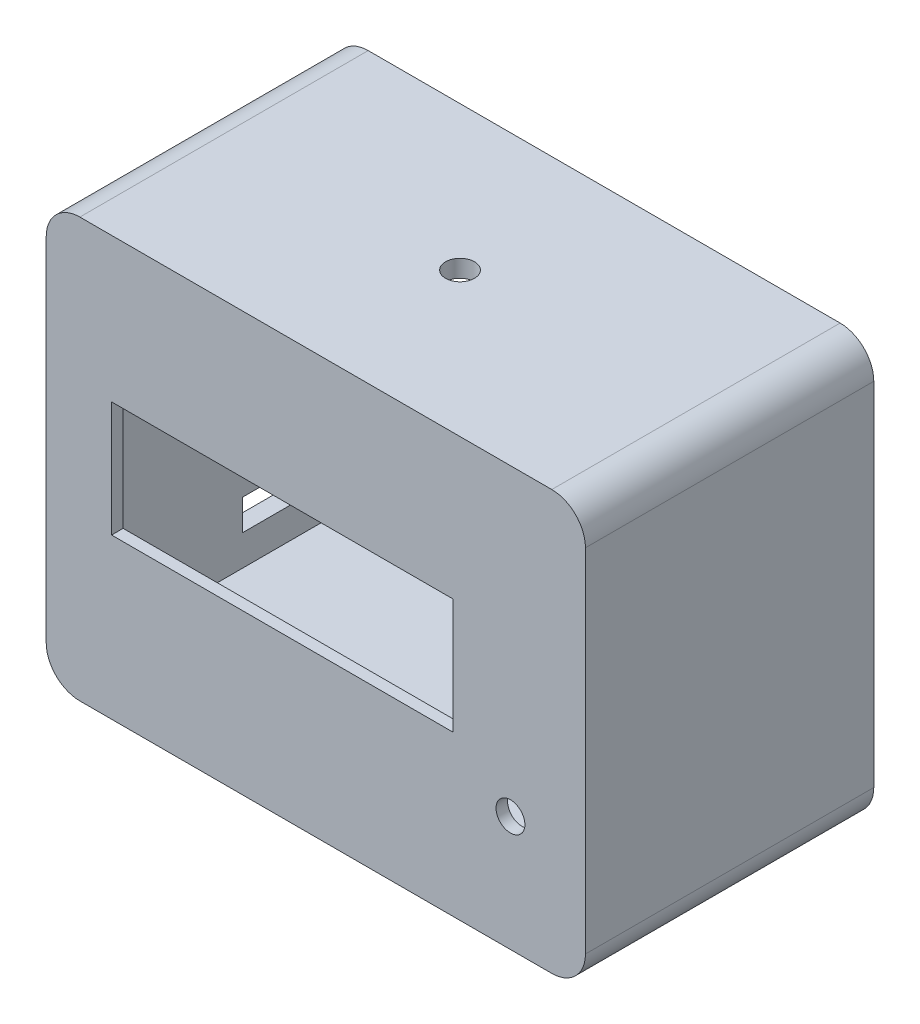
SolidWorks part; units mm, degrees
ref_plane "Front Plane" through (0, 0, 0) normal (0, 0, 1) x (1, 0, 0)
ref_plane "Top Plane" through (0, 0, 0) normal (0, 1, 0) x (1, 0, 0)
ref_plane "Right Plane" through (0, 0, 0) normal (1, 0, 0) x (0, 0, -1)
sketch "Sketch2" plane through (0, 0, 0) normal (0, 0, 1) x (1, 0, 0)
  line L1 (-52.8514, 50.3831) -> (59.3486, 50.3831)
  line L2 (-52.8514, 50.3831) -> (-52.8514, -36.8169)
  line L3 (-52.8514, -36.8169) -> (59.3486, -36.8169)
  line L4 (59.3486, 50.3831) -> (59.3486, -36.8169)
  line L5 (-39.2514, 20.3831) -> (31.7486, 20.3831)
  line L6 (-39.2514, 20.3831) -> (-39.2514, -3.6169)
  line L7 (-39.2514, -3.6169) -> (31.7486, -3.6169)
  line L8 (31.7486, 20.3831) -> (31.7486, -3.6169)
  circle A0 centre (43.7486, -12.8169) radius 3
  dimension "D7" = 6
  dimension "D1" = 87.2
  dimension "D2" = 112.2
  dimension "D3" = 30
  dimension "D4" = 13.6
  dimension "D5" = 71
  dimension "D6" = 24
  dimension "D8" = 15.6
  dimension "D9" = 24
extrude "Boss-Extrude2" add sketch "Sketch2" along normal blind 60
sketch "Sketch6" plane through (0, 0, 0) normal (0, 0, -1) x (-1, 0, 0)
  line L0 (-59.3486, 50.3831) -> (52.8514, 50.3831) construction
  line L1 (-55.7486, 46.7831) -> (49.2514, 46.7831)
  line L2 (-55.7486, 46.7831) -> (-55.7486, -33.2169)
  line L3 (-55.7486, -33.2169) -> (49.2514, -33.2169)
  line L4 (49.2514, 46.7831) -> (49.2514, -33.2169)
  line L5 (52.8514, 50.3831) -> (52.8514, -36.8169) construction
  line L6 (52.8514, -36.8169) -> (-59.3486, -36.8169) construction
  line L7 (-59.3486, -36.8169) -> (-59.3486, 50.3831) construction
  dimension "D1" = 3.6
  dimension "D2" = 3.6
  dimension "D3" = 3.6
  dimension "D4" = 3.6
extrude "Cut-Extrude4" cut sketch "Sketch6" against normal blind 57.6
fillet "Fillet2" radius 7 4 edges at (-52.8514, -36.8169, 30) (59.3486, -36.8169, 30) (-52.8514, 50.3831, 30) (59.3486, 50.3831, 30)
sketch "Sketch7" plane through (0, 50.3831, 0) normal (0, 1, 0) x (1, 0, 0)
  line L0 (52.3486, 0) -> (-45.8514, 0) construction
  line L1 (-52.8514, -60) -> (-52.8514, 0) construction
  circle A0 centre (3.2486, -30) radius 3
  dimension "D1" = 6
  dimension "D2" = 30
  dimension "D3" = 56.1
extrude "Cut-Extrude5" cut sketch "Sketch7" against normal up to next
sketch "Sketch8" plane through (-52.8514, 0, 0) normal (-1, 0, 0) x (0, 0, 1)
  line L0 (0, 43.3831) -> (0, -29.8169) construction
  line L1 (3.4, -20.4242) -> (22.8, -20.4242)
  line L2 (3.4, -20.4242) -> (3.4, -26.8242)
  line L3 (3.4, -26.8242) -> (22.8, -26.8242)
  line L4 (22.8, -20.4242) -> (22.8, -26.8242)
  line L5 (60, -36.8169) -> (0, -36.8169) construction
  dimension "D1" = 3.4
  dimension "D2" = 9.9927
  dimension "D3" = 6.4
  dimension "D4" = 19.4
extrude "Cut-Extrude6" cut sketch "Sketch8" against normal up to next
sketch "Sketch10" plane through (59.3486, 0, 0) normal (1, 0, 0) x (0, 0, -1)
  line L0 (-60, -29.8169) -> (0, -29.8169) construction
  line L1 (-60, -29.8169) -> (-60, 43.3831) construction
  circle A0 centre (-52, -25.8169) radius 1
  dimension "D1" = 2
  dimension "D2" = 4
  dimension "D3" = 8
